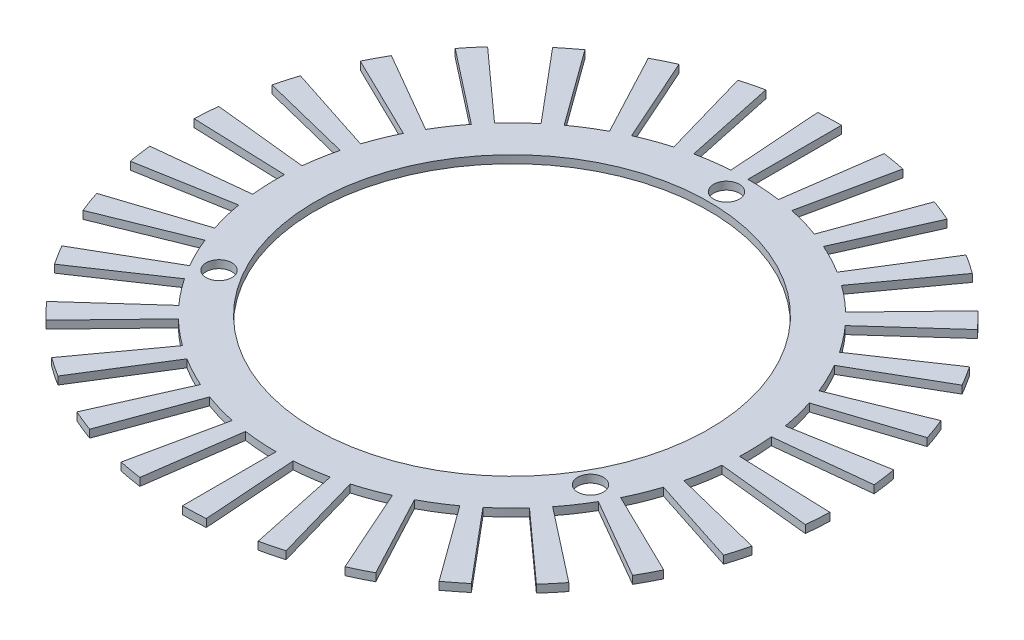
SolidWorks part; units mm, degrees
material "AISI 1010 Steel, hot rolled bar"
ref_plane "Front Plane" through (0, 0, 0) normal (0, 0, 1) x (1, 0, 0)
ref_plane "Top Plane" through (0, 0, 0) normal (0, 1, 0) x (1, 0, 0)
ref_plane "Right Plane" through (0, 0, 0) normal (1, 0, 0) x (0, 0, -1)
sketch "Sketch1" plane through (0, 0, 0) normal (0, 1, 0) x (1, 0, 0)
  circle A0 centre (0, 0) radius 25.25
  dimension "D1" = 50.5
extrude "Extrude-Thin1" add sketch "Sketch1" against normal blind 1 thin
sketch "Sketch2" plane through (0, 0, 0) normal (0, 1, 0) x (1, 0, 0)
  line L0 (0, -30.25) -> (0, 30.25) construction
  line L1 (0, 0) -> (23.8157, -13.75) construction
  line L2 (0, 0) -> (-23.8157, -13.75) construction
  circle A0 centre (0, 27.5) radius 1.65
  circle A1 centre (0, 0) radius 30.25 construction
  circle A4 centre (0, 0) radius 27.5 construction
  circle A7 centre (23.8157, -13.75) radius 1.65
  circle A8 centre (-23.8157, -13.75) radius 1.65
  dimension "D1" = 55
  dimension "D2" = 3.3
  dimension "D3" = 120
  dimension "D4" = 120
extrude "Cut-Extrude3" cut sketch "Sketch2" against normal blind 10
sketch "Sketch5" plane through (0, -1, 0) normal (0, -1, 0) x (1, 0, 0)
  line L0 (0, 0) -> (0, 35.9971) construction
  line L1 (0, 0) -> (2.3792, 34.0237) construction
  line L2 (0, 42.25) -> (0, 30.25)
  line L3 (2.1101, 30.1763) -> (2.9472, 42.1471)
  line L4 (8.7843, 41.3267) -> (6.2893, 29.589)
  line L5 (8.338, 29.0782) -> (11.6457, 40.6133)
  line L6 (17.1846, 38.5973) -> (12.3038, 27.6348)
  line L7 (14.2015, 26.7092) -> (19.8352, 37.3045)
  line L8 (24.8339, 34.181) -> (17.7805, 24.4728)
  line L9 (19.4443, 23.1728) -> (27.1578, 32.3654)
  line L10 (31.3979, 28.2708) -> (22.4801, 20.2412)
  line L11 (23.8373, 18.6238) -> (33.2935, 26.0117)
  line L12 (36.5896, 21.125) -> (26.1973, 15.125)
  line L13 (27.1885, 13.2607) -> (37.974, 18.5212)
  line L14 (40.1821, 13.056) -> (28.7695, 9.3478)
  line L15 (29.3514, 7.3181) -> (40.995, 10.2212)
  line L16 (42.0186, 4.4163) -> (30.0843, 3.162)
  line L17 (30.2316, 1.0557) -> (42.2243, 1.4745)
  line L18 (42.0186, -4.4163) -> (30.0843, -3.162)
  line L19 (29.7904, -5.2529) -> (41.6081, -7.3366)
  line L20 (40.1821, -13.056) -> (28.7695, -9.3478)
  line L21 (28.0473, -11.3318) -> (39.1735, -15.8271)
  line L48 (36.5896, -21.125) -> (26.1973, -15.125)
  line L49 (25.0784, -16.9156) -> (35.0268, -23.6259)
  line L50 (31.3979, -28.2708) -> (22.4801, -20.2412)
  line L51 (21.0134, -21.76) -> (29.3493, -30.3921)
  line L52 (24.8339, -34.181) -> (17.7805, -24.4728)
  line L53 (16.0301, -25.6535) -> (22.3891, -35.83)
  line L54 (17.1846, -38.5973) -> (12.3038, -27.6348)
  line L55 (10.3461, -28.4257) -> (14.4504, -39.702)
  line L56 (8.7843, -41.3267) -> (6.2893, -29.589)
  line L57 (4.21, -29.9556) -> (5.8801, -41.8388)
  line L58 (0, -42.25) -> (0, -30.25)
  line L59 (-2.1101, -30.1763) -> (-2.9472, -42.1471)
  line L60 (-8.7843, -41.3267) -> (-6.2893, -29.589)
  line L61 (-8.338, -29.0782) -> (-11.6457, -40.6133)
  line L62 (-17.1846, -38.5973) -> (-12.3038, -27.6348)
  line L63 (-14.2015, -26.7092) -> (-19.8352, -37.3045)
  line L64 (-24.8339, -34.181) -> (-17.7805, -24.4728)
  line L65 (-19.4443, -23.1728) -> (-27.1578, -32.3654)
  line L66 (-31.3979, -28.2708) -> (-22.4801, -20.2412)
  line L67 (-23.8373, -18.6238) -> (-33.2935, -26.0117)
  line L68 (-36.5896, -21.125) -> (-26.1973, -15.125)
  line L69 (-27.1885, -13.2607) -> (-37.974, -18.5212)
  line L70 (-40.1821, -13.056) -> (-28.7695, -9.3478)
  line L71 (-29.3514, -7.3181) -> (-40.995, -10.2212)
  line L72 (-42.0186, -4.4163) -> (-30.0843, -3.162)
  line L73 (-30.2316, -1.0557) -> (-42.2243, -1.4745)
  line L74 (-42.0186, 4.4163) -> (-30.0843, 3.162)
  line L75 (-29.7904, 5.2529) -> (-41.6081, 7.3366)
  line L76 (-40.1821, 13.056) -> (-28.7695, 9.3478)
  line L77 (-28.0473, 11.3318) -> (-39.1735, 15.8271)
  line L78 (-36.5896, 21.125) -> (-26.1973, 15.125)
  line L79 (-25.0784, 16.9156) -> (-35.0268, 23.6259)
  line L80 (-31.3979, 28.2708) -> (-22.4801, 20.2412)
  line L81 (-21.0134, 21.76) -> (-29.3493, 30.3921)
  line L82 (-24.8339, 34.181) -> (-17.7805, 24.4728)
  line L83 (-16.0301, 25.6535) -> (-22.3891, 35.83)
  line L84 (-17.1846, 38.5973) -> (-12.3038, 27.6348)
  line L85 (-10.3461, 28.4257) -> (-14.4504, 39.702)
  line L86 (-8.7843, 41.3267) -> (-6.2893, 29.589)
  line L87 (-4.21, 29.9556) -> (-5.8801, 41.8388)
  circle A0 centre (0, 0) radius 30.25 construction
  arc A1 (2.1101, 30.1763) -> (0, 30.25) centre (0, 0) ccw
  arc A2 (2.9472, 42.1471) -> (0, 42.25) centre (0, 0) ccw
  arc A3 (11.6457, 40.6133) -> (8.7843, 41.3267) centre (0, 0) ccw
  arc A4 (8.338, 29.0782) -> (6.2893, 29.589) centre (0, 0) ccw
  arc A5 (19.8352, 37.3045) -> (17.1846, 38.5973) centre (0, 0) ccw
  arc A6 (14.2015, 26.7092) -> (12.3038, 27.6348) centre (0, 0) ccw
  arc A7 (27.1578, 32.3654) -> (24.8339, 34.181) centre (0, 0) ccw
  arc A8 (19.4443, 23.1728) -> (17.7805, 24.4728) centre (0, 0) ccw
  arc A9 (33.2935, 26.0117) -> (31.3979, 28.2708) centre (0, 0) ccw
  arc A10 (23.8373, 18.6238) -> (22.4801, 20.2412) centre (0, 0) ccw
  arc A11 (37.974, 18.5212) -> (36.5896, 21.125) centre (0, 0) ccw
  arc A12 (27.1885, 13.2607) -> (26.1973, 15.125) centre (0, 0) ccw
  arc A13 (40.995, 10.2212) -> (40.1821, 13.056) centre (0, 0) ccw
  arc A14 (29.3514, 7.3181) -> (28.7695, 9.3478) centre (0, 0) ccw
  arc A15 (42.2243, 1.4745) -> (42.0186, 4.4163) centre (0, 0) ccw
  arc A16 (30.2316, 1.0557) -> (30.0843, 3.162) centre (0, 0) ccw
  arc A17 (41.6081, -7.3366) -> (42.0186, -4.4163) centre (0, 0) ccw
  arc A18 (29.7904, -5.2529) -> (30.0843, -3.162) centre (0, 0) ccw
  arc A19 (39.1735, -15.8271) -> (40.1821, -13.056) centre (0, 0) ccw
  arc A20 (28.0473, -11.3318) -> (28.7695, -9.3478) centre (0, 0) ccw
  arc A47 (35.0268, -23.6259) -> (36.5896, -21.125) centre (0, 0) ccw
  arc A48 (25.0784, -16.9156) -> (26.1973, -15.125) centre (0, 0) ccw
  arc A49 (29.3493, -30.3921) -> (31.3979, -28.2708) centre (0, 0) ccw
  arc A50 (21.0134, -21.76) -> (22.4801, -20.2412) centre (0, 0) ccw
  arc A51 (22.3891, -35.83) -> (24.8339, -34.181) centre (0, 0) ccw
  arc A52 (16.0301, -25.6535) -> (17.7805, -24.4728) centre (0, 0) ccw
  arc A53 (14.4504, -39.702) -> (17.1846, -38.5973) centre (0, 0) ccw
  arc A54 (10.3461, -28.4257) -> (12.3038, -27.6348) centre (0, 0) ccw
  arc A55 (5.8801, -41.8388) -> (8.7843, -41.3267) centre (0, 0) ccw
  arc A56 (4.21, -29.9556) -> (6.2893, -29.589) centre (0, 0) ccw
  arc A57 (-2.9472, -42.1471) -> (0, -42.25) centre (0, 0) ccw
  arc A58 (-2.1101, -30.1763) -> (0, -30.25) centre (0, 0) ccw
  arc A59 (-11.6457, -40.6133) -> (-8.7843, -41.3267) centre (0, 0) ccw
  arc A60 (-8.338, -29.0782) -> (-6.2893, -29.589) centre (0, 0) ccw
  arc A61 (-19.8352, -37.3045) -> (-17.1846, -38.5973) centre (0, 0) ccw
  arc A62 (-14.2015, -26.7092) -> (-12.3038, -27.6348) centre (0, 0) ccw
  arc A63 (-27.1578, -32.3654) -> (-24.8339, -34.181) centre (0, 0) ccw
  arc A64 (-19.4443, -23.1728) -> (-17.7805, -24.4728) centre (0, 0) ccw
  arc A65 (-33.2935, -26.0117) -> (-31.3979, -28.2708) centre (0, 0) ccw
  arc A66 (-23.8373, -18.6238) -> (-22.4801, -20.2412) centre (0, 0) ccw
  arc A67 (-37.974, -18.5212) -> (-36.5896, -21.125) centre (0, 0) ccw
  arc A68 (-27.1885, -13.2607) -> (-26.1973, -15.125) centre (0, 0) ccw
  arc A69 (-40.995, -10.2212) -> (-40.1821, -13.056) centre (0, 0) ccw
  arc A70 (-29.3514, -7.3181) -> (-28.7695, -9.3478) centre (0, 0) ccw
  arc A71 (-42.2243, -1.4745) -> (-42.0186, -4.4163) centre (0, 0) ccw
  arc A72 (-30.2316, -1.0557) -> (-30.0843, -3.162) centre (0, 0) ccw
  arc A73 (-41.6081, 7.3366) -> (-42.0186, 4.4163) centre (0, 0) ccw
  arc A74 (-29.7904, 5.2529) -> (-30.0843, 3.162) centre (0, 0) ccw
  arc A75 (-39.1735, 15.8271) -> (-40.1821, 13.056) centre (0, 0) ccw
  arc A76 (-28.0473, 11.3318) -> (-28.7695, 9.3478) centre (0, 0) ccw
  arc A77 (-35.0268, 23.6259) -> (-36.5896, 21.125) centre (0, 0) ccw
  arc A78 (-25.0784, 16.9156) -> (-26.1973, 15.125) centre (0, 0) ccw
  arc A79 (-29.3493, 30.3921) -> (-31.3979, 28.2708) centre (0, 0) ccw
  arc A80 (-21.0134, 21.76) -> (-22.4801, 20.2412) centre (0, 0) ccw
  arc A81 (-22.3891, 35.83) -> (-24.8339, 34.181) centre (0, 0) ccw
  arc A82 (-16.0301, 25.6535) -> (-17.7805, 24.4728) centre (0, 0) ccw
  arc A83 (-14.4504, 39.702) -> (-17.1846, 38.5973) centre (0, 0) ccw
  arc A84 (-10.3461, 28.4257) -> (-12.3038, 27.6348) centre (0, 0) ccw
  arc A85 (-5.8801, 41.8388) -> (-8.7843, 41.3267) centre (0, 0) ccw
  arc A86 (-4.21, 29.9556) -> (-6.2893, 29.589) centre (0, 0) ccw
  point P87 (0, 0)
  dimension "D2" = 12
  dimension "D1" = 4
  dimension "D3" = 30
extrude "Boss-Extrude1" add sketch "Sketch5" against normal blind 1
